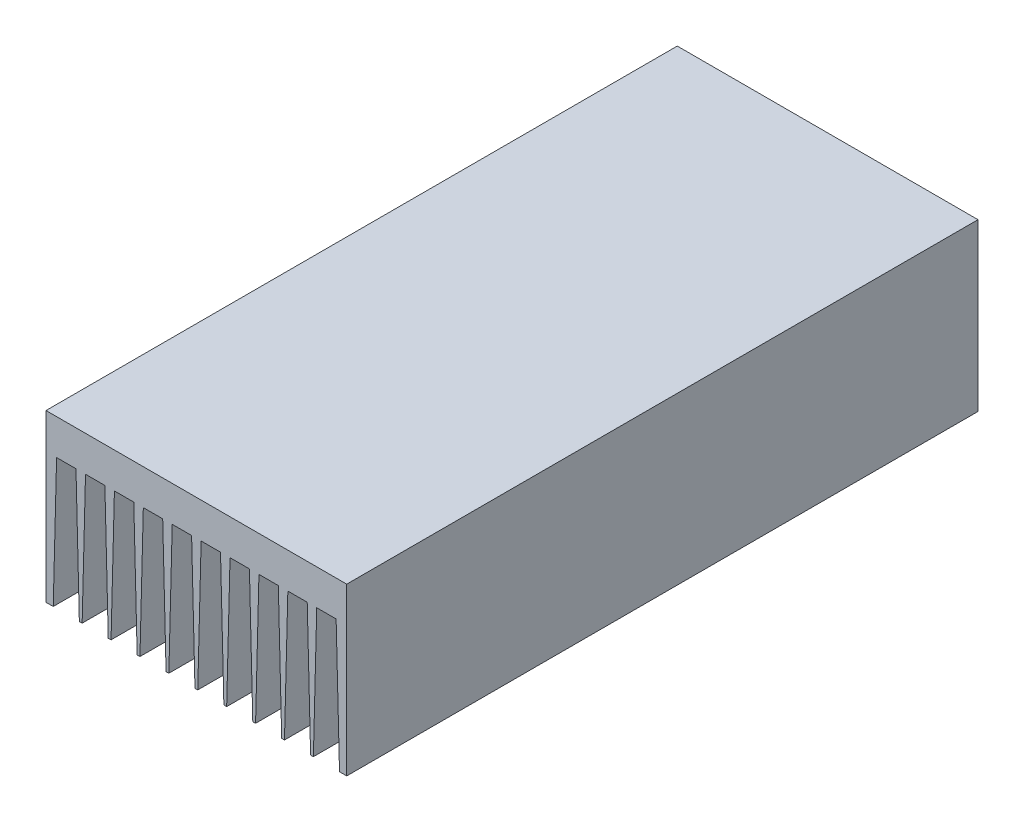
SolidWorks part; units mm, degrees
ref_plane "Plano frontal" through (0, 0, 0) normal (0, 0, 1) x (1, 0, 0)
ref_plane "Plano superior" through (0, 0, 0) normal (0, 1, 0) x (1, 0, 0)
ref_plane "Plano direito" through (0, 0, 0) normal (1, 0, 0) x (0, 0, -1)
sketch "Esboço1" plane through (0, 0, 0) normal (0, 0, 1) x (1, 0, 0)
  line L0 (0, 75) -> (135.77, 75)
  line L1 (135.77, 75) -> (135.77, 0)
  line L2 (0, 75) -> (0, 0)
  line L3 (0, 0) -> (135.77, 0) construction
  line L4 (0, 59) -> (4.785, 59) construction
  line L46 (4.785, 59) -> (13.535, 59)
  line L47 (13.535, 59) -> (17.835, 59) construction
  line L48 (17.835, 59) -> (26.585, 59)
  line L49 (26.585, 59) -> (30.885, 59) construction
  line L50 (30.885, 59) -> (39.635, 59)
  line L51 (39.635, 59) -> (43.935, 59) construction
  line L52 (43.935, 59) -> (52.685, 59)
  line L53 (52.685, 59) -> (56.985, 59) construction
  line L54 (56.985, 59) -> (65.735, 59)
  line L55 (65.735, 59) -> (70.035, 59) construction
  line L56 (70.035, 59) -> (78.785, 59)
  line L57 (78.785, 59) -> (83.085, 59) construction
  line L58 (83.085, 59) -> (91.835, 59)
  line L59 (91.835, 59) -> (96.135, 59) construction
  line L60 (96.135, 59) -> (104.885, 59)
  line L61 (104.885, 59) -> (109.185, 59) construction
  line L62 (109.185, 59) -> (117.935, 59)
  line L63 (117.935, 59) -> (122.235, 59) construction
  line L64 (122.235, 59) -> (130.985, 59)
  line L65 (130.985, 59) -> (135.77, 59) construction
  line L66 (4.785, 59) -> (3.2658, 0)
  line L67 (3.2658, 0) -> (0, 0)
  line L68 (13.535, 59) -> (15.0542, 0)
  line L69 (15.0542, 0) -> (16.3158, 0)
  line L70 (16.3158, 0) -> (17.835, 59)
  line L71 (26.585, 59) -> (28.1042, 0)
  line L72 (28.1042, 0) -> (29.3658, 0)
  line L73 (29.3658, 0) -> (30.885, 59)
  line L74 (39.635, 59) -> (41.1542, 0)
  line L75 (41.1542, 0) -> (42.4158, 0)
  line L76 (42.4158, 0) -> (43.935, 59)
  line L77 (52.685, 59) -> (54.2042, 0)
  line L78 (54.2042, 0) -> (55.4658, 0)
  line L79 (55.4658, 0) -> (56.985, 59)
  line L80 (65.735, 59) -> (67.2542, 0)
  line L81 (67.2542, 0) -> (68.5158, 0)
  line L82 (68.5158, 0) -> (70.035, 59)
  line L83 (78.785, 59) -> (80.3042, 0)
  line L84 (80.3042, 0) -> (81.5658, 0)
  line L85 (81.5658, 0) -> (83.085, 59)
  line L86 (91.835, 59) -> (93.3542, 0)
  line L87 (93.3542, 0) -> (94.6158, 0)
  line L88 (94.6158, 0) -> (96.135, 59)
  line L89 (104.885, 59) -> (106.4042, 0)
  line L90 (106.4042, 0) -> (107.6658, 0)
  line L91 (107.6658, 0) -> (109.185, 59)
  line L92 (117.935, 59) -> (119.4542, 0)
  line L93 (119.4542, 0) -> (120.7158, 0)
  line L94 (120.7158, 0) -> (122.235, 59)
  line L95 (130.985, 59) -> (132.5042, 0)
  line L96 (132.5042, 0) -> (135.77, 0)
  line L97 (67.885, 59) -> (67.885, 75) construction
  line L98 (15.685, 0) -> (15.685, 59) construction
  dimension "D1" = 135.77
  dimension "D2" = 75
  dimension "D3" = 8.75
  dimension "D4" = 4.3
  dimension "D5" = 16
  dimension "D6" = 2.95
extrude "Ressalto-extrusão1" add sketch "Esboço1" along normal blind 285
